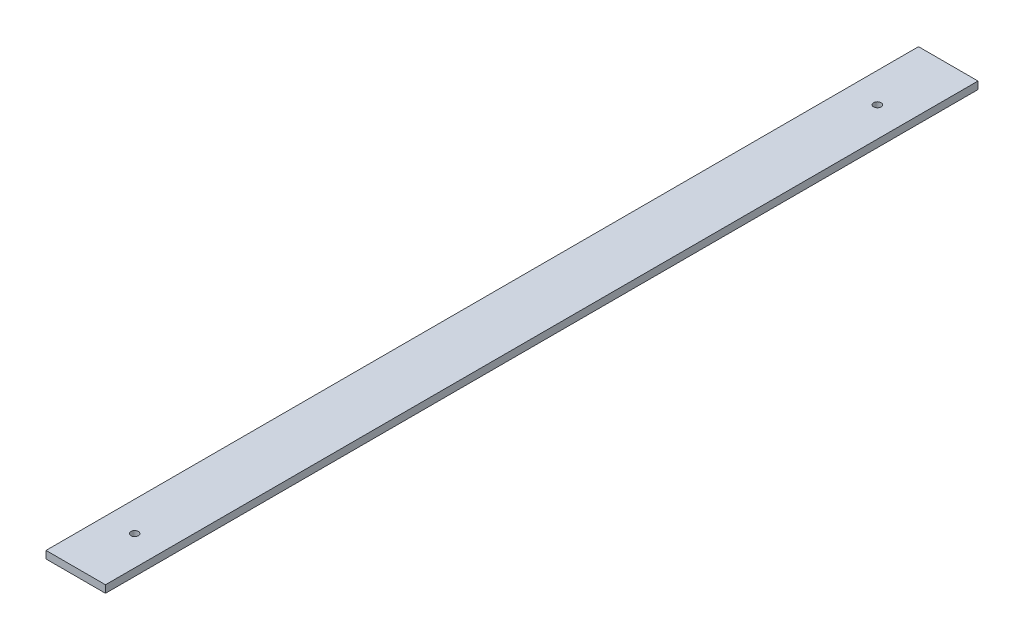
SolidWorks part; units mm, degrees
material "6063-O"
ref_plane "Front Plane" through (0, 0, 0) normal (0, 0, 1) x (1, 0, 0)
ref_plane "Top Plane" through (0, 0, 0) normal (0, 1, 0) x (1, 0, 0)
ref_plane "Right Plane" through (0, 0, 0) normal (1, 0, 0) x (0, 0, -1)
sketch "Sketch4" plane through (0, 0, 0) normal (0, 1, 0) x (1, 0, 0)
  line L4 (23232.9446, -10111.0305) -> (23232.9446, -10251.0305) construction
  line L5 (23232.9446, -9942.5829) -> (23032.9446, -9942.5829)
  line L6 (23232.9446, -9942.5829) -> (23232.9446, -12876.1567)
  line L7 (23232.9446, -12876.1567) -> (23032.9446, -12876.1567)
  line L8 (23032.9446, -9942.5829) -> (23032.9446, -12876.1567)
  line L9 (22132.9446, -9942.5829) -> (21932.9446, -9942.5829)
  line L10 (22132.9446, -9942.5829) -> (22132.9446, -12833.5838)
  line L11 (22132.9446, -12833.5838) -> (21932.9446, -12833.5838)
  line L12 (21932.9446, -9942.5829) -> (21932.9446, -12833.5838)
  line L13 (20932.9446, -9942.5829) -> (20732.9446, -9942.5829)
  line L14 (20932.9446, -9942.5829) -> (20932.9446, -12599.4325)
  line L15 (20932.9446, -12599.4325) -> (20732.9446, -12599.4325)
  line L16 (20732.9446, -9942.5829) -> (20732.9446, -12599.4325)
  line L17 (19732.9446, -9942.5829) -> (19532.9446, -9942.5829)
  line L18 (19732.9446, -9942.5829) -> (19732.9446, -12109.8436)
  line L19 (19732.9446, -12109.8436) -> (19532.9446, -12109.8436)
  line L20 (19532.9446, -9942.5829) -> (19532.9446, -12109.8436)
  line L21 (18902.9446, -9942.5829) -> (18702.9446, -9942.5829)
  line L22 (18902.9446, -9942.5829) -> (18902.9446, -11636.2195)
  line L23 (18902.9446, -11636.2195) -> (18702.9446, -11636.2195)
  line L24 (18702.9446, -9942.5829) -> (18702.9446, -11636.2195)
  line L25 (18702.9446, -10111.0305) -> (18702.9446, -10251.0305) construction
  line L26 (23132.9446, -12748.1199) -> (23132.9446, -12608.0593) construction
  line L27 (22032.9446, -12550.6075) -> (22032.9446, -12691.8491) construction
  line L28 (20832.9446, -12422.3488) -> (20832.9446, -12275.1597) construction
  line L29 (19632.9446, -11906.9658) -> (19632.9446, -11746.8651) construction
  line L30 (18802.9446, -11371.765) -> (18802.9446, -11195.5746) construction
  line L31 (23132.9446, -10251.0305) -> (23132.9446, -10111.0305) construction
  line L32 (18702.9446, -10251.0305) -> (23232.9446, -10251.0305) construction
  line L33 (23232.9446, -10111.0305) -> (18702.9446, -10111.0305) construction
  circle A0 centre (23132.9446, -12678.0896) radius 12.5
  arc A1 (18702.9446, -11295.1434) -> (23232.9446, -12744.4799) centre (22932.9446, -5878.0705) ccw construction
  arc A2 (18702.9446, -11116.3765) -> (23232.9446, -12604.3436) centre (22932.9446, -5878.0705) ccw construction
  circle A3 centre (22032.9446, -12621.2283) radius 12.5
  circle A4 centre (20832.9446, -12348.7542) radius 12.5
  circle A5 centre (19632.9446, -11826.9154) radius 12.5
  circle A6 centre (18802.9446, -11283.6698) radius 12.5
  circle A7 centre (18802.9446, -10181.0305) radius 12.5
  circle A8 centre (19632.9446, -10181.0305) radius 12.5
  circle A9 centre (20832.9446, -10181.0305) radius 12.5
  circle A10 centre (22032.9446, -10181.0305) radius 12.5
  circle A11 centre (23132.9446, -10181.0305) radius 12.5
  arc A12 (18702.9446, -11116.3765) -> (23232.9446, -12604.3436) centre (22932.9446, -5878.0705) ccw construction
  point P22 (23132.9446, -9942.5829)
  point P23 (22032.9446, -9942.5829)
  point P24 (20832.9446, -9942.5829)
  point P25 (19632.9446, -9942.5829)
  point P26 (23132.9446, -12876.1567)
  point P30 (20832.9446, -12599.4325)
  point P40 (23132.9446, -12678.0896)
  point P59 (22032.9446, -12621.2283)
  point P60 (22032.9446, -12833.5838)
  point P68 (20832.9446, -12348.7542)
  point P69 (19632.9446, -12109.8436)
  point P73 (19632.9446, -11826.9154)
  point P74 (18802.9446, -11283.6698)
  point P75 (18802.9446, -11636.2195)
  point P78 (23132.9446, -10181.0305)
  point P91 (18802.9446, -9942.5829)
  dimension "D5" = 25
  dimension "D1" = 200
  dimension "D2" = 1200
  dimension "D3" = 1200
  dimension "D4" = 1200
  dimension "D6" = 100
  dimension "D7" = 70
extrude "Boss-Extrude1" add sketch "Sketch4" along normal blind 25
sketch "Sketch5" plane through (0, 0, 0) normal (0, 1, 0) x (1, 0, 0)
  line L1 (22466.0802, -13868.0747) -> (17213.7932, -13868.0747)
  line L2 (22466.0802, -13868.0747) -> (22466.0802, -8774.4137)
  line L3 (22466.0802, -8774.4137) -> (17213.7932, -8774.4137)
  line L4 (17213.7932, -13868.0747) -> (17213.7932, -8774.4137)
extrude "Cut-Extrude3" cut sketch "Sketch5" along normal through all
